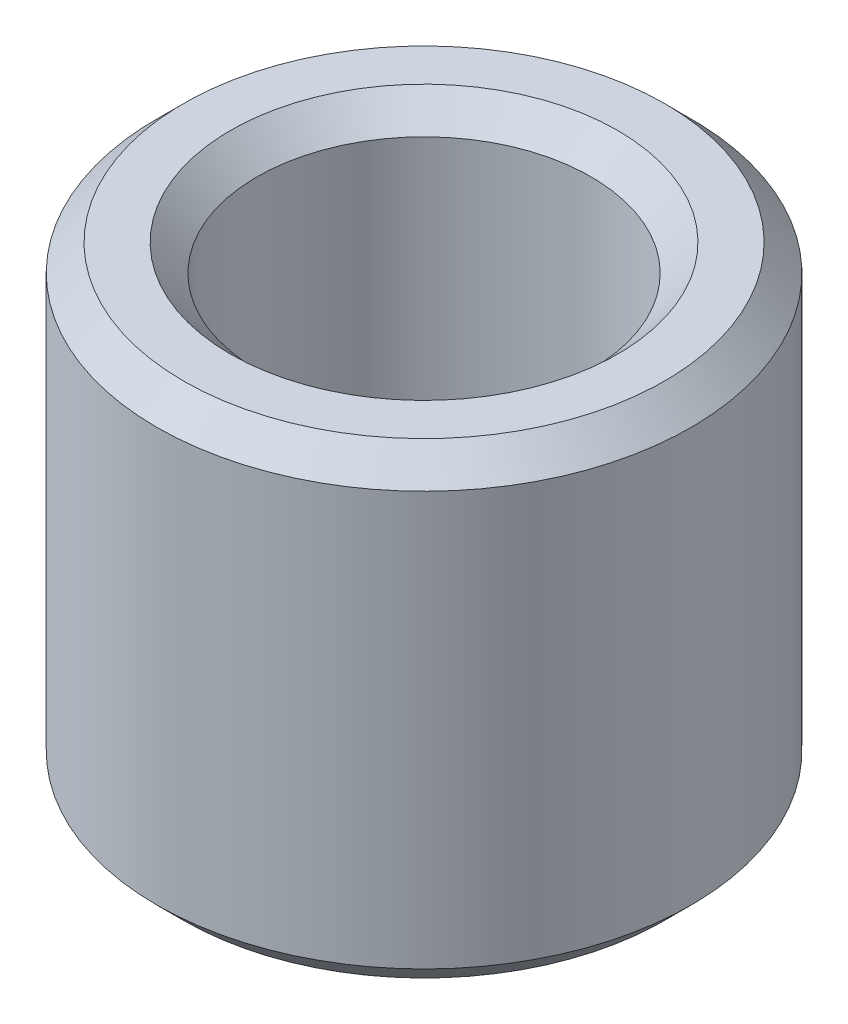
SolidWorks part; units mm, degrees
ref_plane "Front Plane" through (0, 0, 0) normal (0, 0, 1) x (1, 0, 0)
ref_plane "Top Plane" through (0, 0, 0) normal (0, 1, 0) x (1, 0, 0)
ref_plane "Right Plane" through (0, 0, 0) normal (1, 0, 0) x (0, 0, -1)
sketch "Sketch1" plane through (0, 0, 0) normal (0, 1, 0) x (1, 0, 0)
  circle A0 centre (0, 0) radius 1.25
  circle A1 centre (0, 0) radius 2
extrude "Boss-Extrude1" add sketch "Sketch1" along normal blind 3.497
chamfer "Chamfer1" distance 0.2 angle 45 4 edges at (0, 0, 1.25) (0, 3.497, 1.25) (0, 0, 2) (0, 3.497, 2)
